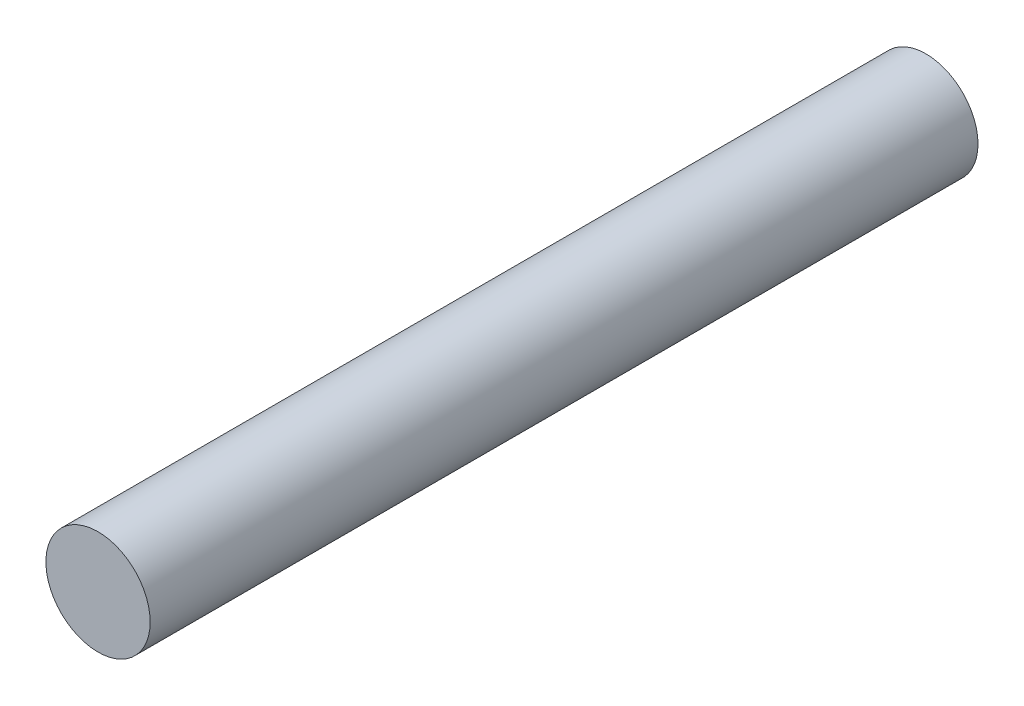
SolidWorks part; units mm, degrees
ref_plane "Front Plane" through (0, 0, 0) normal (0, 0, 1) x (1, 0, 0)
ref_plane "Top Plane" through (0, 0, 0) normal (0, 1, 0) x (1, 0, 0)
ref_plane "Right Plane" through (0, 0, 0) normal (1, 0, 0) x (0, 0, -1)
sketch "Sketch2" plane through (0, 0, 0) normal (0, 0, 1) x (1, 0, 0)
  circle A0 centre (0, 0) radius 1
  dimension "D1" = 2
extrude "Boss-Extrude1" add sketch "Sketch2" along normal mid plane 15.88
